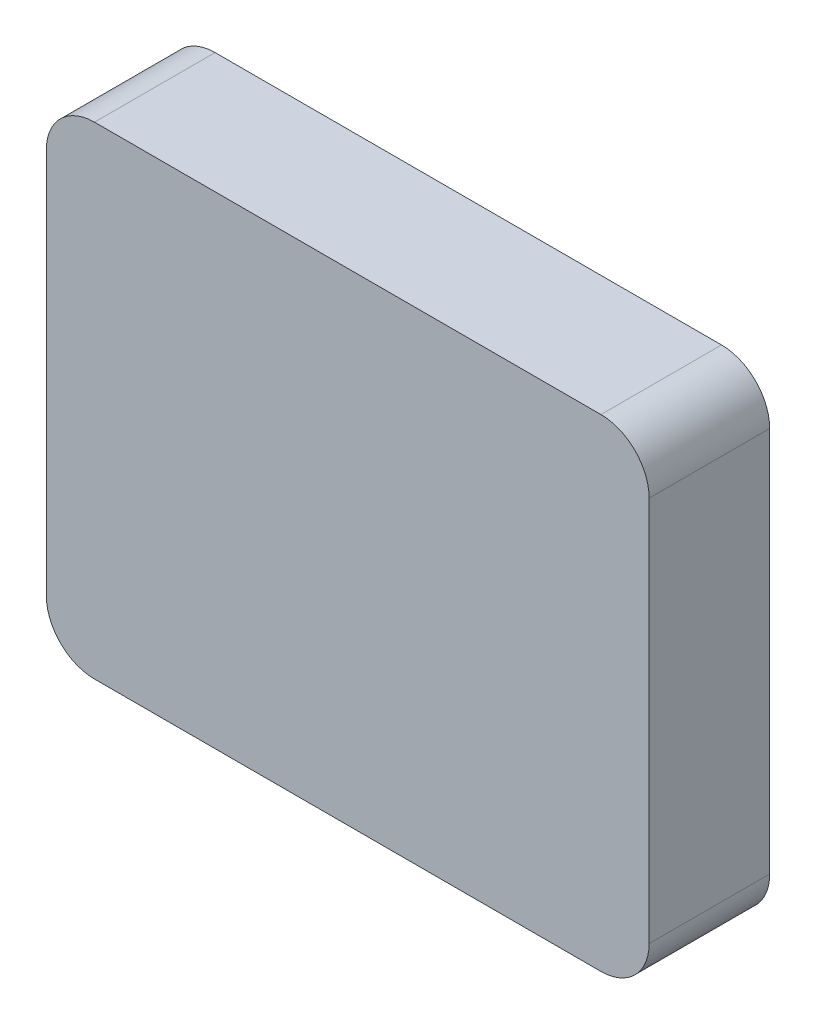
SolidWorks part; units mm, degrees
material "Default"
ref_plane "Front Plane" through (0, 0, 0) normal (0, 0, 1) x (1, 0, 0)
ref_plane "Top Plane" through (0, 0, 0) normal (0, 1, 0) x (1, 0, 0)
ref_plane "Right Plane" through (0, 0, 0) normal (1, 0, 0) x (0, 0, -1)
sketch "Sketch1" plane through (0, 0, 0) normal (0, 0, 1) x (1, 0, 0)
  line L1 (-125, 100) -> (125, 100)
  line L2 (-125, 100) -> (-125, -100)
  line L3 (-125, -100) -> (125, -100)
  line L4 (125, 100) -> (125, -100)
  line L5 (-125, 100) -> (125, -100) construction
  line L6 (-125, -100) -> (125, 100) construction
  point P0 (0, 0)
  dimension "D1" = 250
  dimension "D2" = 200
extrude "Boss-Extrude1" add sketch "Sketch1" along normal mid plane 50
fillet "Fillet1" radius 20 4 edges at (-125, 100, 0) (125, 100, 0) (125, -100, 0) (-125, -100, 0)
